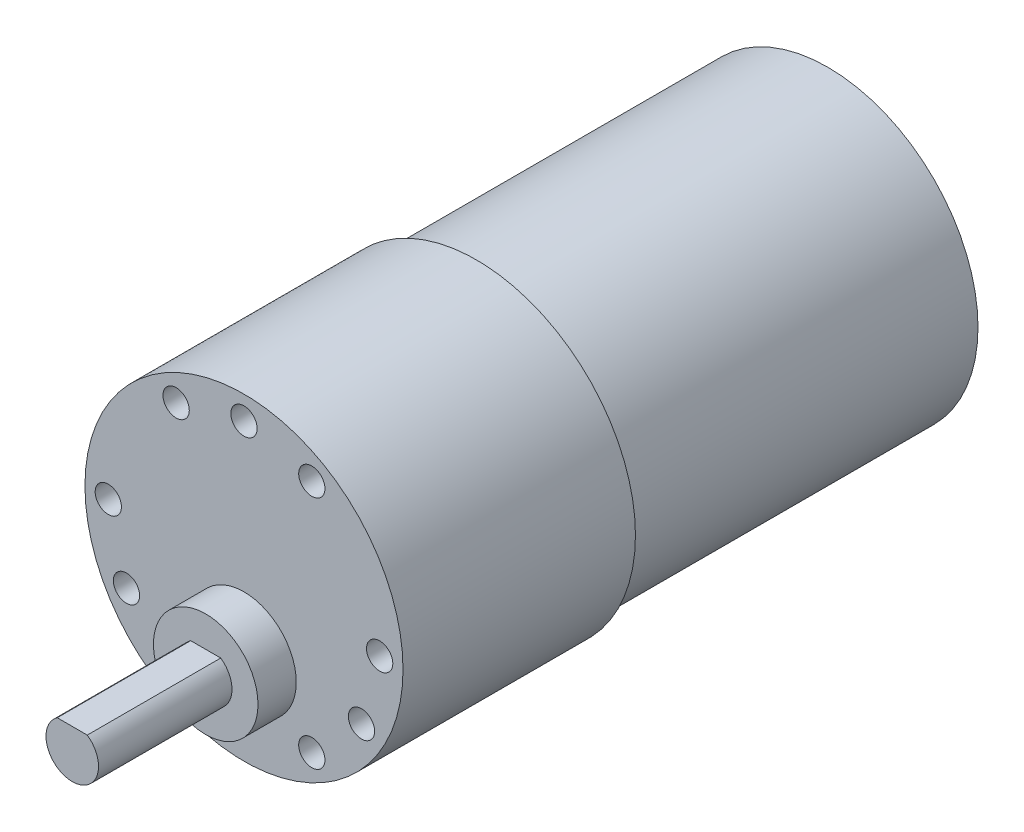
SolidWorks part; units mm, degrees
ref_plane "Front Plane" through (0, 0, 0) normal (0, 0, 1) x (1, 0, 0)
ref_plane "Top Plane" through (0, 0, 0) normal (0, 1, 0) x (1, 0, 0)
ref_plane "Right Plane" through (0, 0, 0) normal (1, 0, 0) x (0, 0, -1)
sketch "Sketch1" plane through (0, 0, 0) normal (0, 0, 1) x (1, 0, 0)
  circle A0 centre (0, 0) radius 18.161
  dimension "D1" = 36.322
extrude "Boss-Extrude1" add sketch "Sketch1" along normal blind 26.543
sketch "Sketch5" plane through (0, 0, 26.543) normal (0, 0, 1) x (1, 0, 0)
  circle A0 centre (0, -7.366) radius 5.969
  dimension "D1" = 11.938
  dimension "D2" = 7.366
extrude "Boss-Extrude5" add sketch "Sketch5" along normal blind 4.3688
sketch "Sketch6" plane through (0, 0, 30.9118) normal (0, 0, 1) x (1, 0, 0)
  line L0 (-1.7157, -4.905) -> (1.7157, -4.905)
  arc A0 (-1.7157, -4.905) -> (1.7157, -4.905) centre (0, -7.366) ccw
  dimension "D1" = 6
  dimension "D2" = 2.461
extrude "Boss-Extrude6" add sketch "Sketch6" along normal blind 15.24
sketch "Sketch9" plane through (0, 0, 26.543) normal (0, 0, 1) x (1, 0, 0)
  line L0 (0, 0) -> (0, 15.494) construction
  circle A0 centre (0, 0) radius 15.494 construction
  dimension "D1" = 30.988
hole_wizard "Ø3.0mm Dowel Hole1" positions "Sketch11" profile "Sketch12" hole size "Ø3.0" standard "ANSI Metric"
sketch "Sketch11" plane through (0, 0, 26.543) normal (0, 0, 1) x (1, 0, 0)
  point P0 (0, 15.494)
sketch "Sketch12" plane through (0, 15.494, 26.543) normal (1, 0, 0) x (0, -1, 0)
  line L0 (0, 0) -> (0, 11.0613)
  line L1 (0, 11.0613) -> (1.5, 10.16)
  line L2 (1.5, 10.16) -> (1.5, 0)
  line L5 (1.5, 0) -> (0, 0)
  line L10 (0, 11.0613) -> (-1.5, 10.16) construction
  line L11 (0, -6.35) -> (0, 107.95) construction
  dimension "Hole Dia." = 3
  dimension "Hole Depth" = 10.16
  dimension "Drill Angle" = 118
pattern_circular "CirPattern2" count 12 over 360 about axis through (0, 0, 0) along (0, 0, 1) skipping 2, 6, 10 of "Ø3.0mm Dowel Hole1"
sketch "Sketch2" plane through (0, 0, 0) normal (0, 0, -1) x (-1, 0, 0)
  circle A0 centre (0, 0) radius 17.145
  dimension "D1" = 34.29
extrude "Boss-Extrude2" add sketch "Sketch2" along normal blind 40.132
sketch "Sketch3" plane through (0, 0, -40.132) normal (0, 0, -1) x (-1, 0, 0)
  circle A0 centre (0, 0) radius 3.048
  dimension "D1" = 6.096
extrude "Boss-Extrude3" add sketch "Sketch3" along normal blind 3.81
sketch "Sketch13" plane through (0, 0, -40.132) normal (0, 0, -1) x (-1, 0, 0)
  circle A0 centre (0, 0) radius 16.637
  dimension "D1" = 33.274
extrude "Cut-Extrude1" cut sketch "Sketch13" against normal blind 1.016
sketch "Sketch14" plane through (0, 0, -39.116) normal (0, 0, -1) x (-1, 0, 0)
  line L0 (0, 0) -> (2.9583, -11.0405) construction
  line L1 (0, 0) -> (-6.5307, -7.783) construction
  circle A0 centre (0, 0) radius 11.43 construction
  circle A1 centre (0, 0) radius 10.16 construction
  dimension "D1" = 22.86
  dimension "D2" = 20.32
ref_plane "Plane1" through (0, 0, 0) normal (0.766, 0.6428, 0) x (0.6428, -0.766, 0)
ref_plane "Plane2" through (0, 0, 0) normal (0.9659, -0.2588, 0) x (-0.2588, -0.9659, 0)
sketch "Sketch15" plane through (0, 0, 0) normal (0.766, 0.6428, 0) x (0.6428, -0.766, 0)
  line L0 (8.89, 39.116) -> (8.89, 44.196)
  line L3 (10.16, 39.116) -> (-10.16, 39.116) construction
  line L4 (8.89, 44.196) -> (11.43, 44.196)
  line L5 (11.43, 44.196) -> (11.43, 39.116)
  line L6 (11.43, 39.116) -> (-11.43, 39.116) construction
  line L7 (11.43, 39.116) -> (8.89, 39.116)
  circle A0 centre (10.16, 42.926) radius 0.4445
  dimension "D4" = 0.889
  dimension "D1" = 5.08
  dimension "D2" = 2.54
  dimension "D3" = 1.27
  dimension "D5" = 1.27
  dimension "D6" = 1.27
extrude "Boss-Extrude7" add sketch "Sketch15" along normal mid plane 0.508
sketch "Sketch16" plane through (0, 0, 0) normal (0.9659, -0.2588, 0) x (-0.2588, -0.9659, 0)
  line L0 (12.7, 39.116) -> (12.7, 44.196)
  line L1 (12.7, 44.196) -> (10.16, 44.196)
  line L2 (10.16, 44.196) -> (10.16, 39.116)
  line L3 (10.16, 39.116) -> (-10.16, 39.116) construction
  line L4 (10.16, 39.116) -> (12.7, 39.116)
  circle A0 centre (11.43, 42.926) radius 0.6786
  dimension "D1" = 1.27
  dimension "D2" = 2.54
  dimension "D3" = 5.08
  dimension "D4" = 1.27
  dimension "D5" = 1.27
extrude "Boss-Extrude8" add sketch "Sketch16" along normal mid plane 0.508
